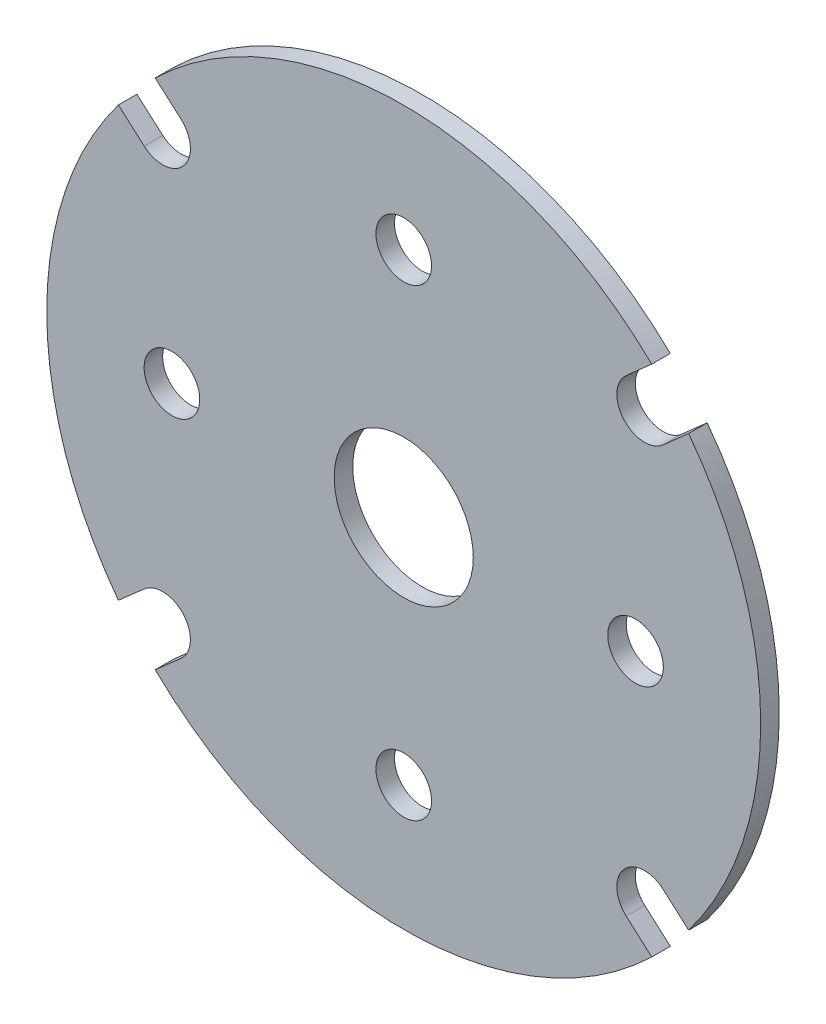
SolidWorks part; units mm, degrees
material "Acrylic (Medium-high impact)"
ref_plane "Front Plane" through (0, 0, 0) normal (0, 0, 1) x (1, 0, 0)
ref_plane "Top Plane" through (0, 0, 0) normal (0, 1, 0) x (1, 0, 0)
ref_plane "Right Plane" through (0, 0, 0) normal (1, 0, 0) x (0, 0, -1)
sketch "Model" plane through (0, 0, 0) normal (0, 0, 1) x (1, 0, 0)
  line L4 (30.7279, -23.1958) -> (27.9693, -20.7537)
  line L5 (26.7508, -27.6884) -> (23.9922, -25.2463)
  line L6 (-30.7735, -23.1353) -> (-27.9907, -20.6815)
  line L7 (-26.8052, -27.6357) -> (-24.0224, -25.1819)
  line L12 (30.7279, 23.1958) -> (27.9693, 20.7537)
  line L13 (26.7508, 27.6884) -> (23.9922, 25.2463)
  line L14 (-30.7735, 23.1353) -> (-27.9907, 20.6815)
  line L15 (-26.8052, 27.6357) -> (-24.0224, 25.1819)
  circle A17 centre (0, 0) radius 7.5
  arc A18 (-26.8052, -27.6357) -> (26.7508, -27.6884) centre (0, 0) ccw
  arc A19 (30.7279, -23.1958) -> (30.7279, 23.1958) centre (0, 0) ccw
  circle A20 centre (0, 25) radius 3
  circle A21 centre (25, 0) radius 3
  circle A22 centre (0, -25) radius 3
  circle A23 centre (-25, 0) radius 3
  arc A24 (27.9693, -20.7537) -> (23.9922, -25.2463) centre (25.9808, -23) ccw
  arc A25 (-24.0224, -25.1819) -> (-27.9907, -20.6815) centre (-26.0066, -22.9317) ccw
  arc A30 (23.9922, 25.2463) -> (27.9693, 20.7537) centre (25.9808, 23) ccw
  arc A31 (-27.9907, 20.6815) -> (-24.0224, 25.1819) centre (-26.0066, 22.9317) ccw
  arc A32 (26.7508, 27.6884) -> (-26.8052, 27.6357) centre (0, 0) ccw
  arc A33 (-30.7735, 23.1353) -> (-30.7735, -23.1353) centre (0, 0) ccw
  dimension "D1" = 6
  dimension "D2" = 15
  dimension "D3" = 38.5
  dimension "D4" = 23.9922
  dimension "D5" = 25
  dimension "D6" = 25.9808
  dimension "D7" = 26.7508
  dimension "D8" = 24.0224
  dimension "D9" = 25
  dimension "D10" = 26.0066
  dimension "D11" = 26.8052
  dimension "D12" = 25
  dimension "D13" = 25
extrude "Boss-Extrude1" add sketch "Model" along normal blind 2
